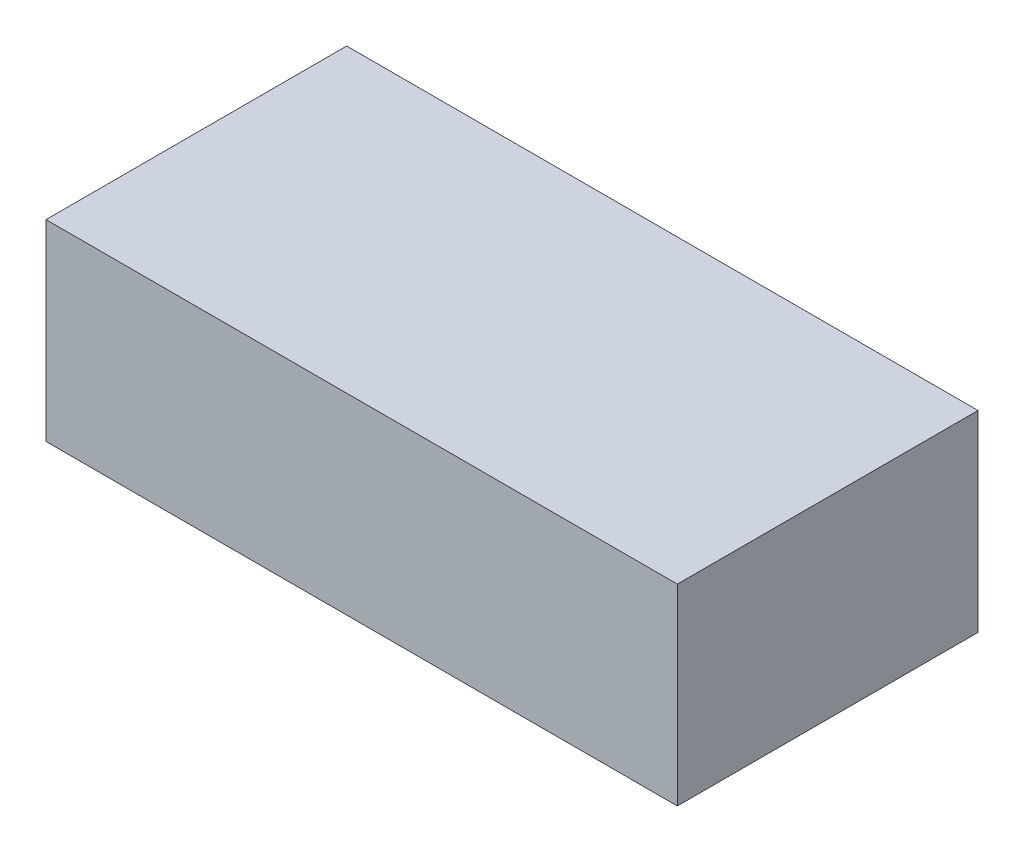
SolidWorks part; units mm, degrees
ref_plane "Front Plane" through (0, 0, 0) normal (0, 0, 1) x (1, 0, 0)
ref_plane "Top Plane" through (0, 0, 0) normal (0, 1, 0) x (1, 0, 0)
ref_plane "Right Plane" through (0, 0, 0) normal (1, 0, 0) x (0, 0, -1)
sketch "Sketch1" plane through (0, 0, 0) normal (0, 1, 0) x (1, 0, 0)
  line L1 (-40, -19.05) -> (40, -19.05)
  line L2 (-40, -19.05) -> (-40, 19.05)
  line L3 (-40, 19.05) -> (40, 19.05)
  line L4 (40, -19.05) -> (40, 19.05)
  line L5 (-40, -19.05) -> (40, 19.05) construction
  line L6 (-40, 19.05) -> (40, -19.05) construction
  point P0 (0, 0)
  dimension "D1" = 80
  dimension "D2" = 38.1
extrude "Boss-Extrude1" add sketch "Sketch1" along normal blind 24.35
